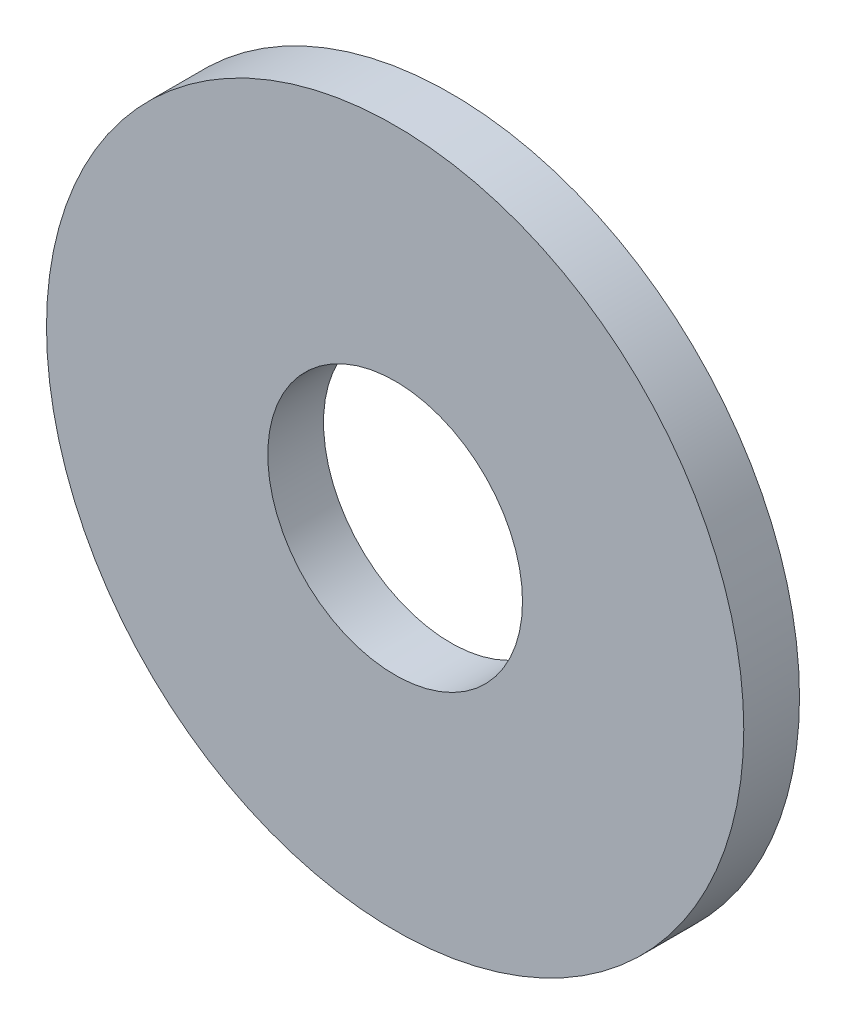
SolidWorks part; units mm, degrees
material "AISI 304"
ref_plane "Front Plane" through (0, 0, 0) normal (0, 0, 1) x (1, 0, 0)
ref_plane "Top Plane" through (0, 0, 0) normal (0, 1, 0) x (1, 0, 0)
ref_plane "Right Plane" through (0, 0, 0) normal (1, 0, 0) x (0, 0, -1)
sketch "body_sketch" plane through (0, 0, 0) normal (0, 0, 1) x (1, 0, 0)
  circle A0 centre (0, 0) radius 4.38
  circle A1 centre (0, 0) radius 1.6
  dimension "OD" = 8.76
  dimension "ID1" = 3.2
extrude "body" add sketch "body_sketch" along normal blind 0.7
